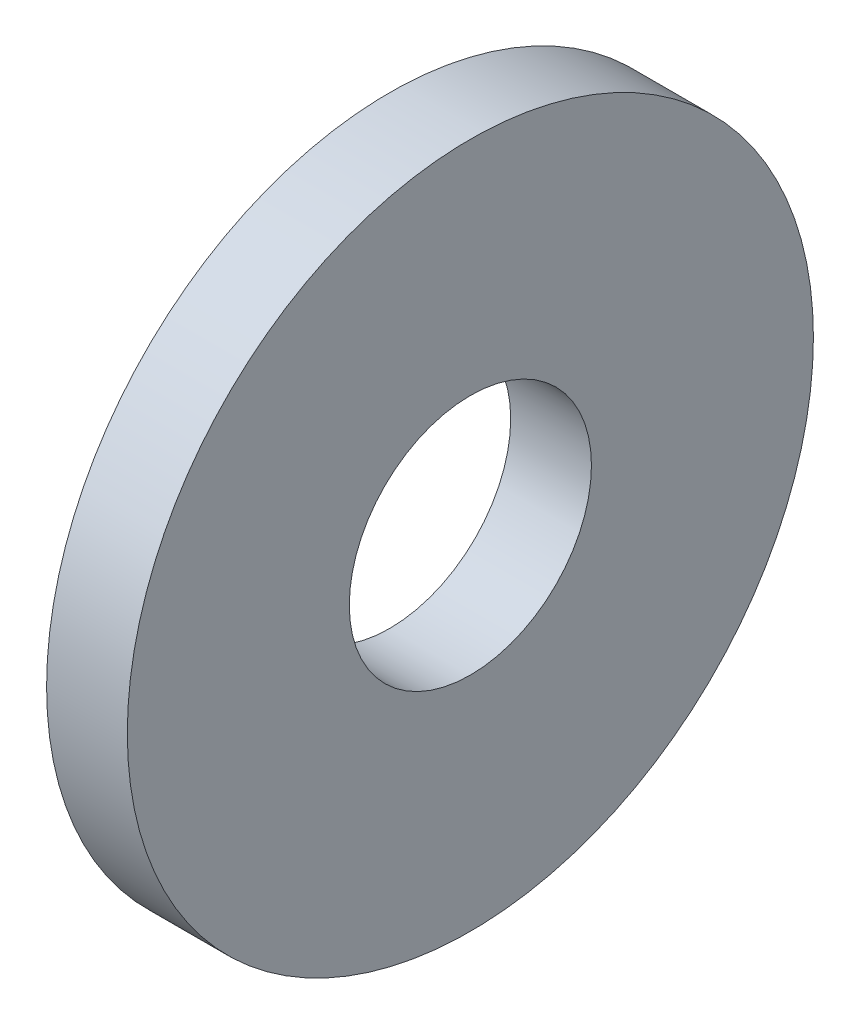
SolidWorks part; units mm, degrees
material "1.0037 (S235JR)"
ref_plane "Front Plane" through (0, 0, 0) normal (0, 0, 1) x (1, 0, 0)
ref_plane "Top Plane" through (0, 0, 0) normal (0, 1, 0) x (1, 0, 0)
ref_plane "Right Plane" through (0, 0, 0) normal (1, 0, 0) x (0, 0, -1)
sketch "Sketch1" plane through (0, 0, 0) normal (1, 0, 0) x (0, 0, -1)
  circle A0 centre (0, 0) radius 17
  dimension "D1" = 34
extrude "Boss-Extrude1" add sketch "Sketch1" along normal mid plane 4
sketch "Sketch2" plane through (0, 0, 0) normal (1, 0, 0) x (0, 0, -1)
  circle A0 centre (0, 0) radius 6
  dimension "D1" = 12
extrude "Cut-Extrude1" cut sketch "Sketch2" against normal through all both and the other way through all
